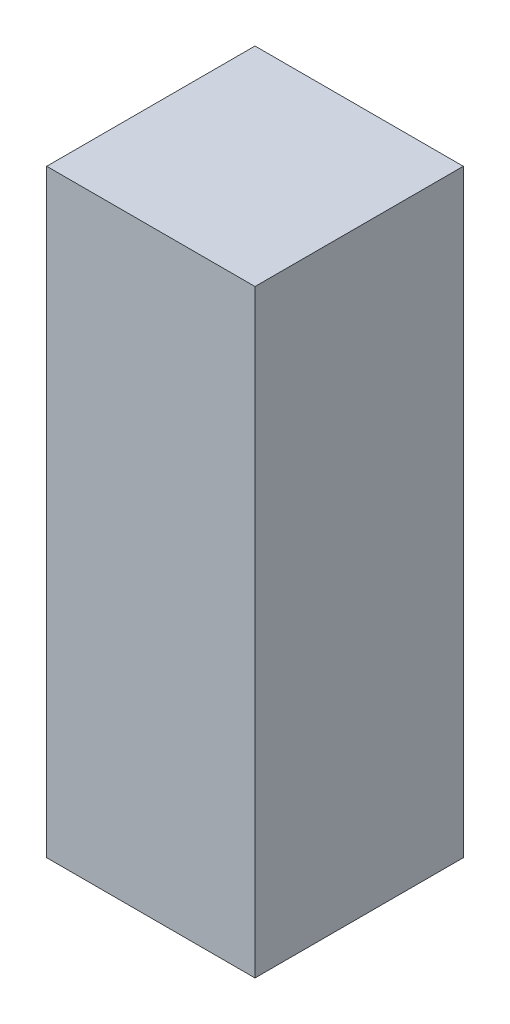
SolidWorks part; units mm, degrees
ref_plane "Спереди" through (0, 0, 0) normal (0, 0, 1) x (1, 0, 0)
ref_plane "Сверху" through (0, 0, 0) normal (0, 1, 0) x (1, 0, 0)
ref_plane "Справа" through (0, 0, 0) normal (1, 0, 0) x (0, 0, -1)
sketch "Эскиз1" plane through (0, 0, 0) normal (1, 0, 0) x (0, 0, -1)
  line L0 (-23.3235, 36.2919) -> (-23.3235, -78.7081) construction
  line L1 (-43.3235, 36.2919) -> (-3.3235, 36.2919)
  line L2 (-43.3235, 36.2919) -> (-43.3235, -78.7081)
  line L3 (-43.3235, -78.7081) -> (-3.3235, -78.7081)
  line L4 (-3.3235, 36.2919) -> (-3.3235, -78.7081)
  dimension "D1" = 115
  dimension "D2" = 40
extrude "Бобышка-Вытянуть1" add sketch "Эскиз1" along normal blind 40
sketch "Эскиз2" plane through (0, 0, 3.3235) normal (0, 0, -1) x (-1, 0, 0)
  line L0 (-20, 36.2919) -> (-20, -78.7081) construction
  line L1 (-40, 36.2919) -> (0, 36.2919) construction
  line L2 (-40, -78.7081) -> (0, -78.7081) construction
  point P7 (-20, -24.7081)
  point P9 (0, 0)
  dimension "D1" = 54
hole_wizard "Отверстие с зазором M31" positions "Эскиз2" profile "Эскиз3" hole size "M3" standard "ISO"
sketch "Эскиз3" plane through (20, -24.7081, 3.3235) normal (1, 0, 0) x (0, 1, 0)
  line L0 (0, 0) -> (0, 6.0215)
  line L1 (0, 6.0215) -> (1.7, 5)
  line L2 (1.7, 5) -> (1.7, 0)
  line L5 (1.7, 0) -> (0, 0)
  line L10 (0, 6.0215) -> (-1.7, 5) construction
  line L11 (0, -6.35) -> (0, 107.95) construction
  dimension "Диаметр отверстия" = 3.4
  dimension "Глубина отверстия" = 5
  dimension "Угол заточки сверла" = 118
sketch "Эскиз4" plane through (0, 0, 3.3235) normal (0, 0, -1) x (-1, 0, 0)
  line L0 (-20, 36.2919) -> (-20, -78.7081) construction
  line L1 (-40, 36.2919) -> (0, 36.2919) construction
  line L2 (-40, -78.7081) -> (0, -78.7081) construction
  point P6 (-20, -43.7081)
  dimension "D1" = 19
hole_wizard "Отверстие с зазором M61" positions "Эскиз4" profile "Эскиз5" hole size "M6" standard "ISO"
sketch "Эскиз5" plane through (20, -43.7081, 3.3235) normal (1, 0, 0) x (0, 1, 0)
  line L0 (0, 0) -> (0, 6.9828)
  line L1 (0, 6.9828) -> (3.3, 5)
  line L2 (3.3, 5) -> (3.3, 0)
  line L5 (3.3, 0) -> (0, 0)
  line L10 (0, 6.9828) -> (-3.3, 5) construction
  line L11 (0, -6.35) -> (0, 107.95) construction
  dimension "Диаметр отверстия" = 6.6
  dimension "Глубина отверстия" = 5
  dimension "Угол заточки сверла" = 118
